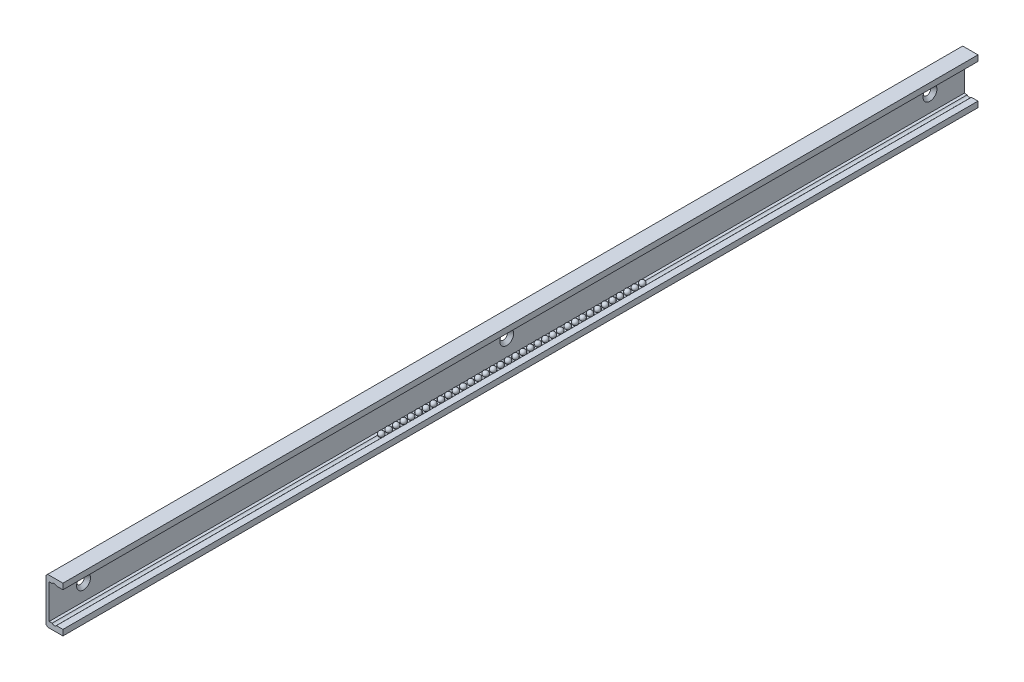
SolidWorks part; units mm, degrees
ref_plane "Front Plane" through (0, 0, 0) normal (0, 0, 1) x (1, 0, 0)
ref_plane "Top Plane" through (0, 0, 0) normal (0, 1, 0) x (1, 0, 0)
ref_plane "Right Plane" through (0, 0, 0) normal (1, 0, 0) x (0, 0, -1)
ref_plane "Plane1" through (0, 0, 0) normal (0, 0, 1) x (1, 0, 0)
sketch "Sketch1" plane through (0, 0, 0) normal (0, 0, 1) x (1, 0, 0)
  line L0 (-7.4, 0.7071) -> (-6.6929, 0)
  line L1 (-6.6929, 0) -> (0, 0)
  line L2 (0, 0) -> (0, 2.5)
  line L3 (0, 2.5) -> (-2.8633, 2.5)
  line L4 (-4.7367, 2.5) -> (-6, 2.5)
  line L5 (-6, 2.5) -> (-6, 17.5)
  line L6 (-6, 17.5) -> (-4.7367, 17.5)
  line L7 (-2.8633, 17.5) -> (0, 17.5)
  line L8 (0, 17.5) -> (0, 20)
  line L9 (0, 20) -> (-6.6929, 20)
  line L10 (-6.6929, 20) -> (-7.4, 19.2929)
  line L11 (-7.4, 19.2929) -> (-7.4, 0.7071)
  arc A0 (-2.8633, 2.5) -> (-4.7367, 2.5) centre (-3.8, 3.25) cw
  arc A1 (-4.7367, 17.5) -> (-2.8633, 17.5) centre (-3.8, 16.75) cw
extrude "Boss-Extrude1" add sketch "Sketch1" along normal blind 400
ref_plane "Plane2" through (0, 0, 15) normal (0, 0, 1) x (1, 0, 0)
sketch "Sketch2" plane through (0, 0, 15) normal (0, 0, 1) x (1, 0, 0)
  line L0 (-7.4, 10) -> (-7.4, 11.65)
  line L1 (-7.4, 11.65) -> (-6, 13.05)
  line L2 (-6, 13.05) -> (-6, 10)
  line L3 (-6, 10) -> (-7.4, 10)
  line L4 (-6, 10) -> (-7.4, 10) construction
revolve "Cut-Revolve1" cut sketch "Sketch2" angle 360 about L4
ref_plane "Plane3" through (0, 0, 385) normal (0, 0, 1) x (1, 0, 0)
sketch "Sketch3" plane through (0, 0, 385) normal (0, 0, 1) x (1, 0, 0)
  line L0 (-7.4, 10) -> (-7.4, 11.65)
  line L1 (-7.4, 11.65) -> (-6, 13.05)
  line L2 (-6, 13.05) -> (-6, 10)
  line L3 (-6, 10) -> (-7.4, 10)
  line L4 (-6, 10) -> (-7.4, 10) construction
revolve "Cut-Revolve2" cut sketch "Sketch3" angle 360 about L4
ref_plane "Plane4" through (0, 0, 200) normal (0, 0, 1) x (1, 0, 0)
sketch "Sketch4" plane through (0, 0, 200) normal (0, 0, 1) x (1, 0, 0)
  line L0 (-7.4, 10) -> (-7.4, 11.65)
  line L1 (-7.4, 11.65) -> (-6, 13.05)
  line L2 (-6, 13.05) -> (-6, 10)
  line L3 (-6, 10) -> (-7.4, 10)
  line L4 (-6, 10) -> (-7.4, 10) construction
revolve "Cut-Revolve3" cut sketch "Sketch4" angle 360 about L4
ref_plane "Plane5" through (0, 3.15, 0) normal (0, 1, 0) x (1, 0, 0)
sketch "Sketch5" plane through (0, 3.15, 0) normal (0, 1, 0) x (1, 0, 0)
  line L0 (-3.8, -144.15) -> (-3.8, -141.75)
  line L1 (-3.8, -144.15) -> (-3.8, -141.75) construction
  arc A0 (-3.8, -141.75) -> (-3.8, -144.15) centre (-3.8, -142.95) cw
revolve "Revolve1" add sketch "Sketch5" angle 360 about L1
ref_plane "Plane6" through (0, 3.15, 0) normal (0, 1, 0) x (1, 0, 0)
sketch "Sketch6" plane through (0, 3.15, 0) normal (0, 1, 0) x (1, 0, 0)
  line L0 (-3.8, -147.41) -> (-3.8, -145.01)
  line L1 (-3.8, -147.41) -> (-3.8, -145.01) construction
  arc A0 (-3.8, -145.01) -> (-3.8, -147.41) centre (-3.8, -146.21) cw
revolve "Revolve2" add sketch "Sketch6" angle 360 about L1
ref_plane "Plane7" through (0, 3.15, 0) normal (0, 1, 0) x (1, 0, 0)
sketch "Sketch7" plane through (0, 3.15, 0) normal (0, 1, 0) x (1, 0, 0)
  line L0 (-3.8, -150.67) -> (-3.8, -148.27)
  line L1 (-3.8, -150.67) -> (-3.8, -148.27) construction
  arc A0 (-3.8, -148.27) -> (-3.8, -150.67) centre (-3.8, -149.47) cw
revolve "Revolve3" add sketch "Sketch7" angle 360 about L1
ref_plane "Plane8" through (0, 3.15, 0) normal (0, 1, 0) x (1, 0, 0)
sketch "Sketch8" plane through (0, 3.15, 0) normal (0, 1, 0) x (1, 0, 0)
  line L0 (-3.8, -153.93) -> (-3.8, -151.53)
  line L1 (-3.8, -153.93) -> (-3.8, -151.53) construction
  arc A0 (-3.8, -151.53) -> (-3.8, -153.93) centre (-3.8, -152.73) cw
revolve "Revolve4" add sketch "Sketch8" angle 360 about L1
ref_plane "Plane9" through (0, 3.15, 0) normal (0, 1, 0) x (1, 0, 0)
sketch "Sketch9" plane through (0, 3.15, 0) normal (0, 1, 0) x (1, 0, 0)
  line L0 (-3.8, -157.19) -> (-3.8, -154.79)
  line L1 (-3.8, -157.19) -> (-3.8, -154.79) construction
  arc A0 (-3.8, -154.79) -> (-3.8, -157.19) centre (-3.8, -155.99) cw
revolve "Revolve5" add sketch "Sketch9" angle 360 about L1
ref_plane "Plane10" through (0, 3.15, 0) normal (0, 1, 0) x (1, 0, 0)
sketch "Sketch10" plane through (0, 3.15, 0) normal (0, 1, 0) x (1, 0, 0)
  line L0 (-3.8, -160.45) -> (-3.8, -158.05)
  line L1 (-3.8, -160.45) -> (-3.8, -158.05) construction
  arc A0 (-3.8, -158.05) -> (-3.8, -160.45) centre (-3.8, -159.25) cw
revolve "Revolve6" add sketch "Sketch10" angle 360 about L1
ref_plane "Plane11" through (0, 3.15, 0) normal (0, 1, 0) x (1, 0, 0)
sketch "Sketch11" plane through (0, 3.15, 0) normal (0, 1, 0) x (1, 0, 0)
  line L0 (-3.8, -163.71) -> (-3.8, -161.31)
  line L1 (-3.8, -163.71) -> (-3.8, -161.31) construction
  arc A0 (-3.8, -161.31) -> (-3.8, -163.71) centre (-3.8, -162.51) cw
revolve "Revolve7" add sketch "Sketch11" angle 360 about L1
ref_plane "Plane12" through (0, 3.15, 0) normal (0, 1, 0) x (1, 0, 0)
sketch "Sketch12" plane through (0, 3.15, 0) normal (0, 1, 0) x (1, 0, 0)
  line L0 (-3.8, -166.97) -> (-3.8, -164.57)
  line L1 (-3.8, -166.97) -> (-3.8, -164.57) construction
  arc A0 (-3.8, -164.57) -> (-3.8, -166.97) centre (-3.8, -165.77) cw
revolve "Revolve8" add sketch "Sketch12" angle 360 about L1
ref_plane "Plane13" through (0, 3.15, 0) normal (0, 1, 0) x (1, 0, 0)
sketch "Sketch13" plane through (0, 3.15, 0) normal (0, 1, 0) x (1, 0, 0)
  line L0 (-3.8, -170.23) -> (-3.8, -167.83)
  line L1 (-3.8, -170.23) -> (-3.8, -167.83) construction
  arc A0 (-3.8, -167.83) -> (-3.8, -170.23) centre (-3.8, -169.03) cw
revolve "Revolve9" add sketch "Sketch13" angle 360 about L1
ref_plane "Plane14" through (0, 3.15, 0) normal (0, 1, 0) x (1, 0, 0)
sketch "Sketch14" plane through (0, 3.15, 0) normal (0, 1, 0) x (1, 0, 0)
  line L0 (-3.8, -173.49) -> (-3.8, -171.09)
  line L1 (-3.8, -173.49) -> (-3.8, -171.09) construction
  arc A0 (-3.8, -171.09) -> (-3.8, -173.49) centre (-3.8, -172.29) cw
revolve "Revolve10" add sketch "Sketch14" angle 360 about L1
ref_plane "Plane15" through (0, 3.15, 0) normal (0, 1, 0) x (1, 0, 0)
sketch "Sketch15" plane through (0, 3.15, 0) normal (0, 1, 0) x (1, 0, 0)
  line L0 (-3.8, -176.75) -> (-3.8, -174.35)
  line L1 (-3.8, -176.75) -> (-3.8, -174.35) construction
  arc A0 (-3.8, -174.35) -> (-3.8, -176.75) centre (-3.8, -175.55) cw
revolve "Revolve11" add sketch "Sketch15" angle 360 about L1
ref_plane "Plane16" through (0, 3.15, 0) normal (0, 1, 0) x (1, 0, 0)
sketch "Sketch16" plane through (0, 3.15, 0) normal (0, 1, 0) x (1, 0, 0)
  line L0 (-3.8, -180.01) -> (-3.8, -177.61)
  line L1 (-3.8, -180.01) -> (-3.8, -177.61) construction
  arc A0 (-3.8, -177.61) -> (-3.8, -180.01) centre (-3.8, -178.81) cw
revolve "Revolve12" add sketch "Sketch16" angle 360 about L1
ref_plane "Plane17" through (0, 3.15, 0) normal (0, 1, 0) x (1, 0, 0)
sketch "Sketch17" plane through (0, 3.15, 0) normal (0, 1, 0) x (1, 0, 0)
  line L0 (-3.8, -183.27) -> (-3.8, -180.87)
  line L1 (-3.8, -183.27) -> (-3.8, -180.87) construction
  arc A0 (-3.8, -180.87) -> (-3.8, -183.27) centre (-3.8, -182.07) cw
revolve "Revolve13" add sketch "Sketch17" angle 360 about L1
ref_plane "Plane18" through (0, 3.15, 0) normal (0, 1, 0) x (1, 0, 0)
sketch "Sketch18" plane through (0, 3.15, 0) normal (0, 1, 0) x (1, 0, 0)
  line L0 (-3.8, -186.53) -> (-3.8, -184.13)
  line L1 (-3.8, -186.53) -> (-3.8, -184.13) construction
  arc A0 (-3.8, -184.13) -> (-3.8, -186.53) centre (-3.8, -185.33) cw
revolve "Revolve14" add sketch "Sketch18" angle 360 about L1
ref_plane "Plane19" through (0, 3.15, 0) normal (0, 1, 0) x (1, 0, 0)
sketch "Sketch19" plane through (0, 3.15, 0) normal (0, 1, 0) x (1, 0, 0)
  line L0 (-3.8, -189.79) -> (-3.8, -187.39)
  line L1 (-3.8, -189.79) -> (-3.8, -187.39) construction
  arc A0 (-3.8, -187.39) -> (-3.8, -189.79) centre (-3.8, -188.59) cw
revolve "Revolve15" add sketch "Sketch19" angle 360 about L1
ref_plane "Plane20" through (0, 3.15, 0) normal (0, 1, 0) x (1, 0, 0)
sketch "Sketch20" plane through (0, 3.15, 0) normal (0, 1, 0) x (1, 0, 0)
  line L0 (-3.8, -193.05) -> (-3.8, -190.65)
  line L1 (-3.8, -193.05) -> (-3.8, -190.65) construction
  arc A0 (-3.8, -190.65) -> (-3.8, -193.05) centre (-3.8, -191.85) cw
revolve "Revolve16" add sketch "Sketch20" angle 360 about L1
ref_plane "Plane21" through (0, 3.15, 0) normal (0, 1, 0) x (1, 0, 0)
sketch "Sketch21" plane through (0, 3.15, 0) normal (0, 1, 0) x (1, 0, 0)
  line L0 (-3.8, -196.31) -> (-3.8, -193.91)
  line L1 (-3.8, -196.31) -> (-3.8, -193.91) construction
  arc A0 (-3.8, -193.91) -> (-3.8, -196.31) centre (-3.8, -195.11) cw
revolve "Revolve17" add sketch "Sketch21" angle 360 about L1
ref_plane "Plane22" through (0, 3.15, 0) normal (0, 1, 0) x (1, 0, 0)
sketch "Sketch22" plane through (0, 3.15, 0) normal (0, 1, 0) x (1, 0, 0)
  line L0 (-3.8, -199.57) -> (-3.8, -197.17)
  line L1 (-3.8, -199.57) -> (-3.8, -197.17) construction
  arc A0 (-3.8, -197.17) -> (-3.8, -199.57) centre (-3.8, -198.37) cw
revolve "Revolve18" add sketch "Sketch22" angle 360 about L1
ref_plane "Plane23" through (0, 3.15, 0) normal (0, 1, 0) x (1, 0, 0)
sketch "Sketch23" plane through (0, 3.15, 0) normal (0, 1, 0) x (1, 0, 0)
  line L0 (-3.8, -202.83) -> (-3.8, -200.43)
  line L1 (-3.8, -202.83) -> (-3.8, -200.43) construction
  arc A0 (-3.8, -200.43) -> (-3.8, -202.83) centre (-3.8, -201.63) cw
revolve "Revolve19" add sketch "Sketch23" angle 360 about L1
ref_plane "Plane24" through (0, 3.15, 0) normal (0, 1, 0) x (1, 0, 0)
sketch "Sketch24" plane through (0, 3.15, 0) normal (0, 1, 0) x (1, 0, 0)
  line L0 (-3.8, -206.09) -> (-3.8, -203.69)
  line L1 (-3.8, -206.09) -> (-3.8, -203.69) construction
  arc A0 (-3.8, -203.69) -> (-3.8, -206.09) centre (-3.8, -204.89) cw
revolve "Revolve20" add sketch "Sketch24" angle 360 about L1
ref_plane "Plane25" through (0, 3.15, 0) normal (0, 1, 0) x (1, 0, 0)
sketch "Sketch25" plane through (0, 3.15, 0) normal (0, 1, 0) x (1, 0, 0)
  line L0 (-3.8, -209.35) -> (-3.8, -206.95)
  line L1 (-3.8, -209.35) -> (-3.8, -206.95) construction
  arc A0 (-3.8, -206.95) -> (-3.8, -209.35) centre (-3.8, -208.15) cw
revolve "Revolve21" add sketch "Sketch25" angle 360 about L1
ref_plane "Plane26" through (0, 3.15, 0) normal (0, 1, 0) x (1, 0, 0)
sketch "Sketch26" plane through (0, 3.15, 0) normal (0, 1, 0) x (1, 0, 0)
  line L0 (-3.8, -212.61) -> (-3.8, -210.21)
  line L1 (-3.8, -212.61) -> (-3.8, -210.21) construction
  arc A0 (-3.8, -210.21) -> (-3.8, -212.61) centre (-3.8, -211.41) cw
revolve "Revolve22" add sketch "Sketch26" angle 360 about L1
ref_plane "Plane27" through (0, 3.15, 0) normal (0, 1, 0) x (1, 0, 0)
sketch "Sketch27" plane through (0, 3.15, 0) normal (0, 1, 0) x (1, 0, 0)
  line L0 (-3.8, -215.87) -> (-3.8, -213.47)
  line L1 (-3.8, -215.87) -> (-3.8, -213.47) construction
  arc A0 (-3.8, -213.47) -> (-3.8, -215.87) centre (-3.8, -214.67) cw
revolve "Revolve23" add sketch "Sketch27" angle 360 about L1
ref_plane "Plane28" through (0, 3.15, 0) normal (0, 1, 0) x (1, 0, 0)
sketch "Sketch28" plane through (0, 3.15, 0) normal (0, 1, 0) x (1, 0, 0)
  line L0 (-3.8, -219.13) -> (-3.8, -216.73)
  line L1 (-3.8, -219.13) -> (-3.8, -216.73) construction
  arc A0 (-3.8, -216.73) -> (-3.8, -219.13) centre (-3.8, -217.93) cw
revolve "Revolve24" add sketch "Sketch28" angle 360 about L1
ref_plane "Plane29" through (0, 3.15, 0) normal (0, 1, 0) x (1, 0, 0)
sketch "Sketch29" plane through (0, 3.15, 0) normal (0, 1, 0) x (1, 0, 0)
  line L0 (-3.8, -222.39) -> (-3.8, -219.99)
  line L1 (-3.8, -222.39) -> (-3.8, -219.99) construction
  arc A0 (-3.8, -219.99) -> (-3.8, -222.39) centre (-3.8, -221.19) cw
revolve "Revolve25" add sketch "Sketch29" angle 360 about L1
ref_plane "Plane30" through (0, 3.15, 0) normal (0, 1, 0) x (1, 0, 0)
sketch "Sketch30" plane through (0, 3.15, 0) normal (0, 1, 0) x (1, 0, 0)
  line L0 (-3.8, -225.65) -> (-3.8, -223.25)
  line L1 (-3.8, -225.65) -> (-3.8, -223.25) construction
  arc A0 (-3.8, -223.25) -> (-3.8, -225.65) centre (-3.8, -224.45) cw
revolve "Revolve26" add sketch "Sketch30" angle 360 about L1
ref_plane "Plane31" through (0, 3.15, 0) normal (0, 1, 0) x (1, 0, 0)
sketch "Sketch31" plane through (0, 3.15, 0) normal (0, 1, 0) x (1, 0, 0)
  line L0 (-3.8, -228.91) -> (-3.8, -226.51)
  line L1 (-3.8, -228.91) -> (-3.8, -226.51) construction
  arc A0 (-3.8, -226.51) -> (-3.8, -228.91) centre (-3.8, -227.71) cw
revolve "Revolve27" add sketch "Sketch31" angle 360 about L1
ref_plane "Plane32" through (0, 3.15, 0) normal (0, 1, 0) x (1, 0, 0)
sketch "Sketch32" plane through (0, 3.15, 0) normal (0, 1, 0) x (1, 0, 0)
  line L0 (-3.8, -232.17) -> (-3.8, -229.77)
  line L1 (-3.8, -232.17) -> (-3.8, -229.77) construction
  arc A0 (-3.8, -229.77) -> (-3.8, -232.17) centre (-3.8, -230.97) cw
revolve "Revolve28" add sketch "Sketch32" angle 360 about L1
ref_plane "Plane33" through (0, 3.15, 0) normal (0, 1, 0) x (1, 0, 0)
sketch "Sketch33" plane through (0, 3.15, 0) normal (0, 1, 0) x (1, 0, 0)
  line L0 (-3.8, -235.43) -> (-3.8, -233.03)
  line L1 (-3.8, -235.43) -> (-3.8, -233.03) construction
  arc A0 (-3.8, -233.03) -> (-3.8, -235.43) centre (-3.8, -234.23) cw
revolve "Revolve29" add sketch "Sketch33" angle 360 about L1
ref_plane "Plane34" through (0, 3.15, 0) normal (0, 1, 0) x (1, 0, 0)
sketch "Sketch34" plane through (0, 3.15, 0) normal (0, 1, 0) x (1, 0, 0)
  line L0 (-3.8, -238.69) -> (-3.8, -236.29)
  line L1 (-3.8, -238.69) -> (-3.8, -236.29) construction
  arc A0 (-3.8, -236.29) -> (-3.8, -238.69) centre (-3.8, -237.49) cw
revolve "Revolve30" add sketch "Sketch34" angle 360 about L1
ref_plane "Plane35" through (0, 3.15, 0) normal (0, 1, 0) x (1, 0, 0)
sketch "Sketch35" plane through (0, 3.15, 0) normal (0, 1, 0) x (1, 0, 0)
  line L0 (-3.8, -241.95) -> (-3.8, -239.55)
  line L1 (-3.8, -241.95) -> (-3.8, -239.55) construction
  arc A0 (-3.8, -239.55) -> (-3.8, -241.95) centre (-3.8, -240.75) cw
revolve "Revolve31" add sketch "Sketch35" angle 360 about L1
ref_plane "Plane36" through (0, 3.15, 0) normal (0, 1, 0) x (1, 0, 0)
sketch "Sketch36" plane through (0, 3.15, 0) normal (0, 1, 0) x (1, 0, 0)
  line L0 (-3.8, -245.21) -> (-3.8, -242.81)
  line L1 (-3.8, -245.21) -> (-3.8, -242.81) construction
  arc A0 (-3.8, -242.81) -> (-3.8, -245.21) centre (-3.8, -244.01) cw
revolve "Revolve32" add sketch "Sketch36" angle 360 about L1
ref_plane "Plane37" through (0, 3.15, 0) normal (0, 1, 0) x (1, 0, 0)
sketch "Sketch37" plane through (0, 3.15, 0) normal (0, 1, 0) x (1, 0, 0)
  line L0 (-3.8, -248.47) -> (-3.8, -246.07)
  line L1 (-3.8, -248.47) -> (-3.8, -246.07) construction
  arc A0 (-3.8, -246.07) -> (-3.8, -248.47) centre (-3.8, -247.27) cw
revolve "Revolve33" add sketch "Sketch37" angle 360 about L1
ref_plane "Plane38" through (0, 3.15, 0) normal (0, 1, 0) x (1, 0, 0)
sketch "Sketch38" plane through (0, 3.15, 0) normal (0, 1, 0) x (1, 0, 0)
  line L0 (-3.8, -251.73) -> (-3.8, -249.33)
  line L1 (-3.8, -251.73) -> (-3.8, -249.33) construction
  arc A0 (-3.8, -249.33) -> (-3.8, -251.73) centre (-3.8, -250.53) cw
revolve "Revolve34" add sketch "Sketch38" angle 360 about L1
ref_plane "Plane39" through (0, 3.15, 0) normal (0, 1, 0) x (1, 0, 0)
sketch "Sketch39" plane through (0, 3.15, 0) normal (0, 1, 0) x (1, 0, 0)
  line L0 (-3.8, -254.99) -> (-3.8, -252.59)
  line L1 (-3.8, -254.99) -> (-3.8, -252.59) construction
  arc A0 (-3.8, -252.59) -> (-3.8, -254.99) centre (-3.8, -253.79) cw
revolve "Revolve35" add sketch "Sketch39" angle 360 about L1
ref_plane "Plane40" through (0, 3.15, 0) normal (0, 1, 0) x (1, 0, 0)
sketch "Sketch40" plane through (0, 3.15, 0) normal (0, 1, 0) x (1, 0, 0)
  line L0 (-3.8, -258.25) -> (-3.8, -255.85)
  line L1 (-3.8, -258.25) -> (-3.8, -255.85) construction
  arc A0 (-3.8, -255.85) -> (-3.8, -258.25) centre (-3.8, -257.05) cw
revolve "Revolve36" add sketch "Sketch40" angle 360 about L1
ref_plane "Plane41" through (0, 16.85, 0) normal (0, 1, 0) x (1, 0, 0)
sketch "Sketch41" plane through (0, 16.85, 0) normal (0, 1, 0) x (1, 0, 0)
  line L0 (-3.8, -144.15) -> (-3.8, -141.75)
  line L1 (-3.8, -144.15) -> (-3.8, -141.75) construction
  arc A0 (-3.8, -141.75) -> (-3.8, -144.15) centre (-3.8, -142.95) cw
revolve "Revolve37" add sketch "Sketch41" angle 360 about L1
ref_plane "Plane42" through (0, 16.85, 0) normal (0, 1, 0) x (1, 0, 0)
sketch "Sketch42" plane through (0, 16.85, 0) normal (0, 1, 0) x (1, 0, 0)
  line L0 (-3.8, -147.41) -> (-3.8, -145.01)
  line L1 (-3.8, -147.41) -> (-3.8, -145.01) construction
  arc A0 (-3.8, -145.01) -> (-3.8, -147.41) centre (-3.8, -146.21) cw
revolve "Revolve38" add sketch "Sketch42" angle 360 about L1
ref_plane "Plane43" through (0, 16.85, 0) normal (0, 1, 0) x (1, 0, 0)
sketch "Sketch43" plane through (0, 16.85, 0) normal (0, 1, 0) x (1, 0, 0)
  line L0 (-3.8, -150.67) -> (-3.8, -148.27)
  line L1 (-3.8, -150.67) -> (-3.8, -148.27) construction
  arc A0 (-3.8, -148.27) -> (-3.8, -150.67) centre (-3.8, -149.47) cw
revolve "Revolve39" add sketch "Sketch43" angle 360 about L1
ref_plane "Plane44" through (0, 16.85, 0) normal (0, 1, 0) x (1, 0, 0)
sketch "Sketch44" plane through (0, 16.85, 0) normal (0, 1, 0) x (1, 0, 0)
  line L0 (-3.8, -153.93) -> (-3.8, -151.53)
  line L1 (-3.8, -153.93) -> (-3.8, -151.53) construction
  arc A0 (-3.8, -151.53) -> (-3.8, -153.93) centre (-3.8, -152.73) cw
revolve "Revolve40" add sketch "Sketch44" angle 360 about L1
ref_plane "Plane45" through (0, 16.85, 0) normal (0, 1, 0) x (1, 0, 0)
sketch "Sketch45" plane through (0, 16.85, 0) normal (0, 1, 0) x (1, 0, 0)
  line L0 (-3.8, -157.19) -> (-3.8, -154.79)
  line L1 (-3.8, -157.19) -> (-3.8, -154.79) construction
  arc A0 (-3.8, -154.79) -> (-3.8, -157.19) centre (-3.8, -155.99) cw
revolve "Revolve41" add sketch "Sketch45" angle 360 about L1
ref_plane "Plane46" through (0, 16.85, 0) normal (0, 1, 0) x (1, 0, 0)
sketch "Sketch46" plane through (0, 16.85, 0) normal (0, 1, 0) x (1, 0, 0)
  line L0 (-3.8, -160.45) -> (-3.8, -158.05)
  line L1 (-3.8, -160.45) -> (-3.8, -158.05) construction
  arc A0 (-3.8, -158.05) -> (-3.8, -160.45) centre (-3.8, -159.25) cw
revolve "Revolve42" add sketch "Sketch46" angle 360 about L1
ref_plane "Plane47" through (0, 16.85, 0) normal (0, 1, 0) x (1, 0, 0)
sketch "Sketch47" plane through (0, 16.85, 0) normal (0, 1, 0) x (1, 0, 0)
  line L0 (-3.8, -163.71) -> (-3.8, -161.31)
  line L1 (-3.8, -163.71) -> (-3.8, -161.31) construction
  arc A0 (-3.8, -161.31) -> (-3.8, -163.71) centre (-3.8, -162.51) cw
revolve "Revolve43" add sketch "Sketch47" angle 360 about L1
ref_plane "Plane48" through (0, 16.85, 0) normal (0, 1, 0) x (1, 0, 0)
sketch "Sketch48" plane through (0, 16.85, 0) normal (0, 1, 0) x (1, 0, 0)
  line L0 (-3.8, -166.97) -> (-3.8, -164.57)
  line L1 (-3.8, -166.97) -> (-3.8, -164.57) construction
  arc A0 (-3.8, -164.57) -> (-3.8, -166.97) centre (-3.8, -165.77) cw
revolve "Revolve44" add sketch "Sketch48" angle 360 about L1
ref_plane "Plane49" through (0, 16.85, 0) normal (0, 1, 0) x (1, 0, 0)
sketch "Sketch49" plane through (0, 16.85, 0) normal (0, 1, 0) x (1, 0, 0)
  line L0 (-3.8, -170.23) -> (-3.8, -167.83)
  line L1 (-3.8, -170.23) -> (-3.8, -167.83) construction
  arc A0 (-3.8, -167.83) -> (-3.8, -170.23) centre (-3.8, -169.03) cw
revolve "Revolve45" add sketch "Sketch49" angle 360 about L1
ref_plane "Plane50" through (0, 16.85, 0) normal (0, 1, 0) x (1, 0, 0)
sketch "Sketch50" plane through (0, 16.85, 0) normal (0, 1, 0) x (1, 0, 0)
  line L0 (-3.8, -173.49) -> (-3.8, -171.09)
  line L1 (-3.8, -173.49) -> (-3.8, -171.09) construction
  arc A0 (-3.8, -171.09) -> (-3.8, -173.49) centre (-3.8, -172.29) cw
revolve "Revolve46" add sketch "Sketch50" angle 360 about L1
ref_plane "Plane51" through (0, 16.85, 0) normal (0, 1, 0) x (1, 0, 0)
sketch "Sketch51" plane through (0, 16.85, 0) normal (0, 1, 0) x (1, 0, 0)
  line L0 (-3.8, -176.75) -> (-3.8, -174.35)
  line L1 (-3.8, -176.75) -> (-3.8, -174.35) construction
  arc A0 (-3.8, -174.35) -> (-3.8, -176.75) centre (-3.8, -175.55) cw
revolve "Revolve47" add sketch "Sketch51" angle 360 about L1
ref_plane "Plane52" through (0, 16.85, 0) normal (0, 1, 0) x (1, 0, 0)
sketch "Sketch52" plane through (0, 16.85, 0) normal (0, 1, 0) x (1, 0, 0)
  line L0 (-3.8, -180.01) -> (-3.8, -177.61)
  line L1 (-3.8, -180.01) -> (-3.8, -177.61) construction
  arc A0 (-3.8, -177.61) -> (-3.8, -180.01) centre (-3.8, -178.81) cw
revolve "Revolve48" add sketch "Sketch52" angle 360 about L1
ref_plane "Plane53" through (0, 16.85, 0) normal (0, 1, 0) x (1, 0, 0)
sketch "Sketch53" plane through (0, 16.85, 0) normal (0, 1, 0) x (1, 0, 0)
  line L0 (-3.8, -183.27) -> (-3.8, -180.87)
  line L1 (-3.8, -183.27) -> (-3.8, -180.87) construction
  arc A0 (-3.8, -180.87) -> (-3.8, -183.27) centre (-3.8, -182.07) cw
revolve "Revolve49" add sketch "Sketch53" angle 360 about L1
ref_plane "Plane54" through (0, 16.85, 0) normal (0, 1, 0) x (1, 0, 0)
sketch "Sketch54" plane through (0, 16.85, 0) normal (0, 1, 0) x (1, 0, 0)
  line L0 (-3.8, -186.53) -> (-3.8, -184.13)
  line L1 (-3.8, -186.53) -> (-3.8, -184.13) construction
  arc A0 (-3.8, -184.13) -> (-3.8, -186.53) centre (-3.8, -185.33) cw
revolve "Revolve50" add sketch "Sketch54" angle 360 about L1
ref_plane "Plane55" through (0, 16.85, 0) normal (0, 1, 0) x (1, 0, 0)
sketch "Sketch55" plane through (0, 16.85, 0) normal (0, 1, 0) x (1, 0, 0)
  line L0 (-3.8, -189.79) -> (-3.8, -187.39)
  line L1 (-3.8, -189.79) -> (-3.8, -187.39) construction
  arc A0 (-3.8, -187.39) -> (-3.8, -189.79) centre (-3.8, -188.59) cw
revolve "Revolve51" add sketch "Sketch55" angle 360 about L1
ref_plane "Plane56" through (0, 16.85, 0) normal (0, 1, 0) x (1, 0, 0)
sketch "Sketch56" plane through (0, 16.85, 0) normal (0, 1, 0) x (1, 0, 0)
  line L0 (-3.8, -193.05) -> (-3.8, -190.65)
  line L1 (-3.8, -193.05) -> (-3.8, -190.65) construction
  arc A0 (-3.8, -190.65) -> (-3.8, -193.05) centre (-3.8, -191.85) cw
revolve "Revolve52" add sketch "Sketch56" angle 360 about L1
ref_plane "Plane57" through (0, 16.85, 0) normal (0, 1, 0) x (1, 0, 0)
sketch "Sketch57" plane through (0, 16.85, 0) normal (0, 1, 0) x (1, 0, 0)
  line L0 (-3.8, -196.31) -> (-3.8, -193.91)
  line L1 (-3.8, -196.31) -> (-3.8, -193.91) construction
  arc A0 (-3.8, -193.91) -> (-3.8, -196.31) centre (-3.8, -195.11) cw
revolve "Revolve53" add sketch "Sketch57" angle 360 about L1
ref_plane "Plane58" through (0, 16.85, 0) normal (0, 1, 0) x (1, 0, 0)
sketch "Sketch58" plane through (0, 16.85, 0) normal (0, 1, 0) x (1, 0, 0)
  line L0 (-3.8, -199.57) -> (-3.8, -197.17)
  line L1 (-3.8, -199.57) -> (-3.8, -197.17) construction
  arc A0 (-3.8, -197.17) -> (-3.8, -199.57) centre (-3.8, -198.37) cw
revolve "Revolve54" add sketch "Sketch58" angle 360 about L1
ref_plane "Plane59" through (0, 16.85, 0) normal (0, 1, 0) x (1, 0, 0)
sketch "Sketch59" plane through (0, 16.85, 0) normal (0, 1, 0) x (1, 0, 0)
  line L0 (-3.8, -202.83) -> (-3.8, -200.43)
  line L1 (-3.8, -202.83) -> (-3.8, -200.43) construction
  arc A0 (-3.8, -200.43) -> (-3.8, -202.83) centre (-3.8, -201.63) cw
revolve "Revolve55" add sketch "Sketch59" angle 360 about L1
ref_plane "Plane60" through (0, 16.85, 0) normal (0, 1, 0) x (1, 0, 0)
sketch "Sketch60" plane through (0, 16.85, 0) normal (0, 1, 0) x (1, 0, 0)
  line L0 (-3.8, -206.09) -> (-3.8, -203.69)
  line L1 (-3.8, -206.09) -> (-3.8, -203.69) construction
  arc A0 (-3.8, -203.69) -> (-3.8, -206.09) centre (-3.8, -204.89) cw
revolve "Revolve56" add sketch "Sketch60" angle 360 about L1
ref_plane "Plane61" through (0, 16.85, 0) normal (0, 1, 0) x (1, 0, 0)
sketch "Sketch61" plane through (0, 16.85, 0) normal (0, 1, 0) x (1, 0, 0)
  line L0 (-3.8, -209.35) -> (-3.8, -206.95)
  line L1 (-3.8, -209.35) -> (-3.8, -206.95) construction
  arc A0 (-3.8, -206.95) -> (-3.8, -209.35) centre (-3.8, -208.15) cw
revolve "Revolve57" add sketch "Sketch61" angle 360 about L1
ref_plane "Plane62" through (0, 16.85, 0) normal (0, 1, 0) x (1, 0, 0)
sketch "Sketch62" plane through (0, 16.85, 0) normal (0, 1, 0) x (1, 0, 0)
  line L0 (-3.8, -212.61) -> (-3.8, -210.21)
  line L1 (-3.8, -212.61) -> (-3.8, -210.21) construction
  arc A0 (-3.8, -210.21) -> (-3.8, -212.61) centre (-3.8, -211.41) cw
revolve "Revolve58" add sketch "Sketch62" angle 360 about L1
ref_plane "Plane63" through (0, 16.85, 0) normal (0, 1, 0) x (1, 0, 0)
sketch "Sketch63" plane through (0, 16.85, 0) normal (0, 1, 0) x (1, 0, 0)
  line L0 (-3.8, -215.87) -> (-3.8, -213.47)
  line L1 (-3.8, -215.87) -> (-3.8, -213.47) construction
  arc A0 (-3.8, -213.47) -> (-3.8, -215.87) centre (-3.8, -214.67) cw
revolve "Revolve59" add sketch "Sketch63" angle 360 about L1
ref_plane "Plane64" through (0, 16.85, 0) normal (0, 1, 0) x (1, 0, 0)
sketch "Sketch64" plane through (0, 16.85, 0) normal (0, 1, 0) x (1, 0, 0)
  line L0 (-3.8, -219.13) -> (-3.8, -216.73)
  line L1 (-3.8, -219.13) -> (-3.8, -216.73) construction
  arc A0 (-3.8, -216.73) -> (-3.8, -219.13) centre (-3.8, -217.93) cw
revolve "Revolve60" add sketch "Sketch64" angle 360 about L1
ref_plane "Plane65" through (0, 16.85, 0) normal (0, 1, 0) x (1, 0, 0)
sketch "Sketch65" plane through (0, 16.85, 0) normal (0, 1, 0) x (1, 0, 0)
  line L0 (-3.8, -222.39) -> (-3.8, -219.99)
  line L1 (-3.8, -222.39) -> (-3.8, -219.99) construction
  arc A0 (-3.8, -219.99) -> (-3.8, -222.39) centre (-3.8, -221.19) cw
revolve "Revolve61" add sketch "Sketch65" angle 360 about L1
ref_plane "Plane66" through (0, 16.85, 0) normal (0, 1, 0) x (1, 0, 0)
sketch "Sketch66" plane through (0, 16.85, 0) normal (0, 1, 0) x (1, 0, 0)
  line L0 (-3.8, -225.65) -> (-3.8, -223.25)
  line L1 (-3.8, -225.65) -> (-3.8, -223.25) construction
  arc A0 (-3.8, -223.25) -> (-3.8, -225.65) centre (-3.8, -224.45) cw
revolve "Revolve62" add sketch "Sketch66" angle 360 about L1
ref_plane "Plane67" through (0, 16.85, 0) normal (0, 1, 0) x (1, 0, 0)
sketch "Sketch67" plane through (0, 16.85, 0) normal (0, 1, 0) x (1, 0, 0)
  line L0 (-3.8, -228.91) -> (-3.8, -226.51)
  line L1 (-3.8, -228.91) -> (-3.8, -226.51) construction
  arc A0 (-3.8, -226.51) -> (-3.8, -228.91) centre (-3.8, -227.71) cw
revolve "Revolve63" add sketch "Sketch67" angle 360 about L1
ref_plane "Plane68" through (0, 16.85, 0) normal (0, 1, 0) x (1, 0, 0)
sketch "Sketch68" plane through (0, 16.85, 0) normal (0, 1, 0) x (1, 0, 0)
  line L0 (-3.8, -232.17) -> (-3.8, -229.77)
  line L1 (-3.8, -232.17) -> (-3.8, -229.77) construction
  arc A0 (-3.8, -229.77) -> (-3.8, -232.17) centre (-3.8, -230.97) cw
revolve "Revolve64" add sketch "Sketch68" angle 360 about L1
ref_plane "Plane69" through (0, 16.85, 0) normal (0, 1, 0) x (1, 0, 0)
sketch "Sketch69" plane through (0, 16.85, 0) normal (0, 1, 0) x (1, 0, 0)
  line L0 (-3.8, -235.43) -> (-3.8, -233.03)
  line L1 (-3.8, -235.43) -> (-3.8, -233.03) construction
  arc A0 (-3.8, -233.03) -> (-3.8, -235.43) centre (-3.8, -234.23) cw
revolve "Revolve65" add sketch "Sketch69" angle 360 about L1
ref_plane "Plane70" through (0, 16.85, 0) normal (0, 1, 0) x (1, 0, 0)
sketch "Sketch70" plane through (0, 16.85, 0) normal (0, 1, 0) x (1, 0, 0)
  line L0 (-3.8, -238.69) -> (-3.8, -236.29)
  line L1 (-3.8, -238.69) -> (-3.8, -236.29) construction
  arc A0 (-3.8, -236.29) -> (-3.8, -238.69) centre (-3.8, -237.49) cw
revolve "Revolve66" add sketch "Sketch70" angle 360 about L1
ref_plane "Plane71" through (0, 16.85, 0) normal (0, 1, 0) x (1, 0, 0)
sketch "Sketch71" plane through (0, 16.85, 0) normal (0, 1, 0) x (1, 0, 0)
  line L0 (-3.8, -241.95) -> (-3.8, -239.55)
  line L1 (-3.8, -241.95) -> (-3.8, -239.55) construction
  arc A0 (-3.8, -239.55) -> (-3.8, -241.95) centre (-3.8, -240.75) cw
revolve "Revolve67" add sketch "Sketch71" angle 360 about L1
ref_plane "Plane72" through (0, 16.85, 0) normal (0, 1, 0) x (1, 0, 0)
sketch "Sketch72" plane through (0, 16.85, 0) normal (0, 1, 0) x (1, 0, 0)
  line L0 (-3.8, -245.21) -> (-3.8, -242.81)
  line L1 (-3.8, -245.21) -> (-3.8, -242.81) construction
  arc A0 (-3.8, -242.81) -> (-3.8, -245.21) centre (-3.8, -244.01) cw
revolve "Revolve68" add sketch "Sketch72" angle 360 about L1
ref_plane "Plane73" through (0, 16.85, 0) normal (0, 1, 0) x (1, 0, 0)
sketch "Sketch73" plane through (0, 16.85, 0) normal (0, 1, 0) x (1, 0, 0)
  line L0 (-3.8, -248.47) -> (-3.8, -246.07)
  line L1 (-3.8, -248.47) -> (-3.8, -246.07) construction
  arc A0 (-3.8, -246.07) -> (-3.8, -248.47) centre (-3.8, -247.27) cw
revolve "Revolve69" add sketch "Sketch73" angle 360 about L1
ref_plane "Plane74" through (0, 16.85, 0) normal (0, 1, 0) x (1, 0, 0)
sketch "Sketch74" plane through (0, 16.85, 0) normal (0, 1, 0) x (1, 0, 0)
  line L0 (-3.8, -251.73) -> (-3.8, -249.33)
  line L1 (-3.8, -251.73) -> (-3.8, -249.33) construction
  arc A0 (-3.8, -249.33) -> (-3.8, -251.73) centre (-3.8, -250.53) cw
revolve "Revolve70" add sketch "Sketch74" angle 360 about L1
ref_plane "Plane75" through (0, 16.85, 0) normal (0, 1, 0) x (1, 0, 0)
sketch "Sketch75" plane through (0, 16.85, 0) normal (0, 1, 0) x (1, 0, 0)
  line L0 (-3.8, -254.99) -> (-3.8, -252.59)
  line L1 (-3.8, -254.99) -> (-3.8, -252.59) construction
  arc A0 (-3.8, -252.59) -> (-3.8, -254.99) centre (-3.8, -253.79) cw
revolve "Revolve71" add sketch "Sketch75" angle 360 about L1
ref_plane "Plane76" through (0, 16.85, 0) normal (0, 1, 0) x (1, 0, 0)
sketch "Sketch76" plane through (0, 16.85, 0) normal (0, 1, 0) x (1, 0, 0)
  line L0 (-3.8, -258.25) -> (-3.8, -255.85)
  line L1 (-3.8, -258.25) -> (-3.8, -255.85) construction
  arc A0 (-3.8, -255.85) -> (-3.8, -258.25) centre (-3.8, -257.05) cw
revolve "Revolve72" add sketch "Sketch76" angle 360 about L1
